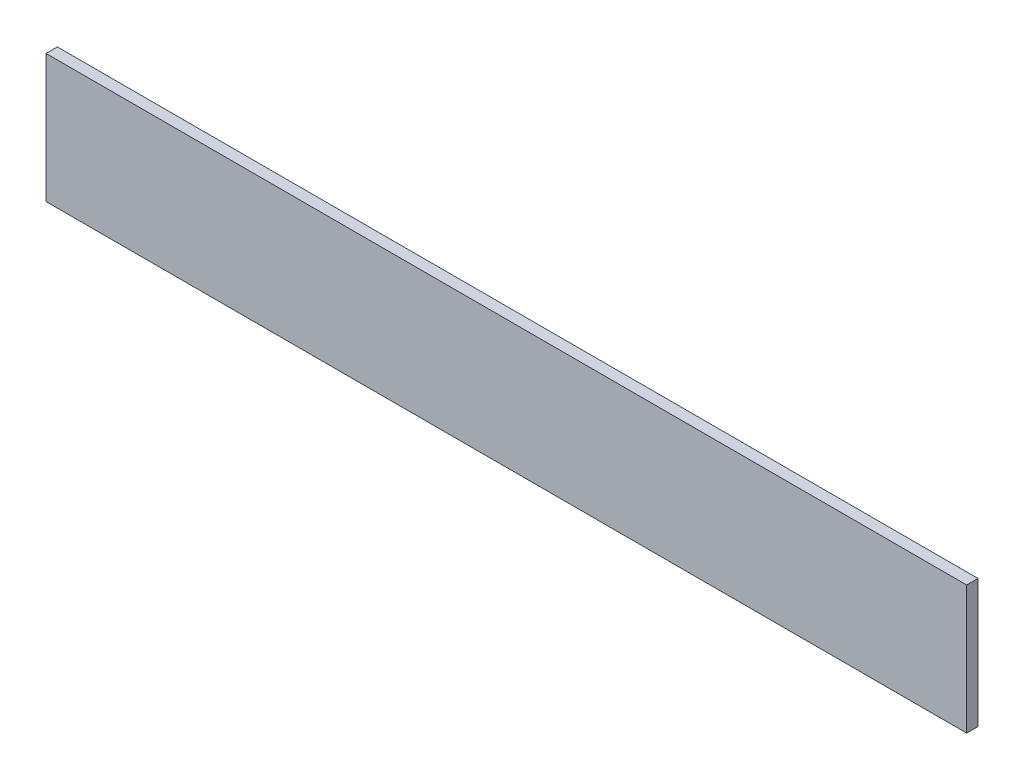
SolidWorks part; units mm, degrees
ref_plane "Front Plane" through (0, 0, 0) normal (0, 0, 1) x (1, 0, 0)
ref_plane "Top Plane" through (0, 0, 0) normal (0, 1, 0) x (1, 0, 0)
ref_plane "Right Plane" through (0, 0, 0) normal (1, 0, 0) x (0, 0, -1)
sketch "Sketch1" plane through (0, 0, 0) normal (0, 0, 1) x (1, 0, 0)
  line L1 (-61, -8.5) -> (61, -8.5)
  line L2 (-61, -8.5) -> (-61, 8.5)
  line L3 (-61, 8.5) -> (61, 8.5)
  line L4 (61, -8.5) -> (61, 8.5)
  line L5 (0, 8.5) -> (0, -8.5) construction
  line L6 (-61, 0) -> (61, 0) construction
  point P0 (0, 0)
  dimension "D1" = 122
  dimension "D2" = 17
extrude "Boss-Extrude1" add sketch "Sketch1" along normal blind 1.5
